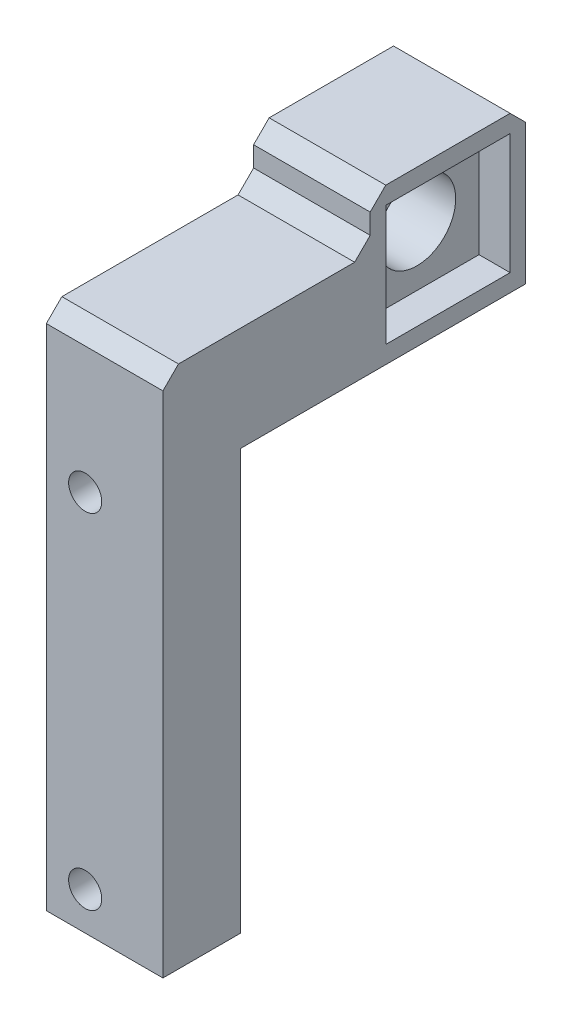
SolidWorks part; units mm, degrees
ref_plane "Front" through (0, 0, 0) normal (0, 0, 1) x (1, 0, 0)
ref_plane "Top" through (0, 0, 0) normal (0, 1, 0) x (1, 0, 0)
ref_plane "Right" through (0, 0, 0) normal (1, 0, 0) x (0, 0, -1)
sketch "Sketch1" plane through (0, 0, 13.4068) normal (0, 0, 1) x (1, 0, 0)
  line L0 (-50, 27) -> (-50, -27)
  line L2 (-50, -27) -> (-35, -27)
  line L3 (-50, 27) -> (-35, 27)
  line L5 (-35, 27) -> (-35, -27)
  circle A1 centre (-45, -22.125) radius 2.1303
  circle A2 centre (-45, 22.125) radius 2.1303
  dimension "D1" = 15
extrude "Boss-Extrude1" add sketch "Sketch1" along normal up to surface (10 mm away)
sketch "Sketch2" plane through (-50, 0, 0) normal (-1, 0, 0) x (0, 0, 1)
  line L0 (23.4068, 27) -> (43.3448, 27) construction
  line L1 (-3.2577, 27) -> (-23.2577, 27)
  line L2 (-3.2577, 27) -> (-3.2577, 47)
  line L3 (-3.2577, 47) -> (-23.2577, 47)
  line L4 (-23.2577, 27) -> (-23.2577, 47)
  line L5 (-23.2577, 27) -> (-3.2577, 47) construction
  circle A0 centre (-13.2577, 37) radius 5
  dimension "D3" = 10
  dimension "D1" = 20
  dimension "D2" = 20
extrude "Boss-Extrude2" add sketch "Sketch2" against normal blind 15
sketch "Sketch5" plane through (-50, 0, 0) normal (-1, 0, 0) x (0, 0, 1)
  line L0 (-3.2577, 27) -> (-3.2577, 47) construction
  line L1 (23.4068, 27) -> (-3.2577, 27)
  line L2 (23.4068, 27) -> (23.4068, 40.4099)
  line L3 (23.4068, 40.4099) -> (-3.2577, 40.4099)
  line L4 (-3.2577, 27) -> (-3.2577, 40.4099)
extrude "Boss-Extrude3" add sketch "Sketch5" against normal up to surface (15 mm away) up to face at (-35, 0, 18.4068)
sketch "Sketch3" plane through (-35, 0, 0) normal (1, 0, 0) x (0, 0, -1)
  line L0 (3.2577, 27) -> (23.2577, 47) construction
  line L1 (5.2577, 29.25) -> (21.2577, 29.25)
  line L2 (5.2577, 29.25) -> (5.2577, 44.75)
  line L3 (5.2577, 44.75) -> (21.2577, 44.75)
  line L4 (21.2577, 29.25) -> (21.2577, 44.75)
  line L5 (23.2577, 47) -> (3.2577, 47) construction
  line L6 (23.2577, 27) -> (23.2577, 47) construction
  line L7 (5.2577, 29.25) -> (21.2577, 44.75) construction
  point P11 (13.2577, 37)
  dimension "D1" = 15.5
  dimension "D2" = 16
extrude "Cut-Extrude2" cut sketch "Sketch3" against normal blind 4
chamfer "Chamfer1" distance 2 angle 45 2 edges at (-42.5, 47, -23.2577) (-42.5, 47, -3.2577)
sketch "Sketch4" plane through (0, 44.75, 0) normal (0, -1, 0) x (-1, 0, 0)
  line L0 (35, 21.2577) -> (35, 5.2577) construction
  circle A0 centre (38, 13.2577) radius 2
  point P6 (35, 13.2577)
  dimension "D1" = 4
  dimension "D2" = 3
extrude "Cut-Extrude3" [suppressed] cut sketch "Sketch4" against normal blind 10
chamfer "Chamfer2" distance 2 angle 45 2 edges at (-42.5, 40.4099, 23.4068)
